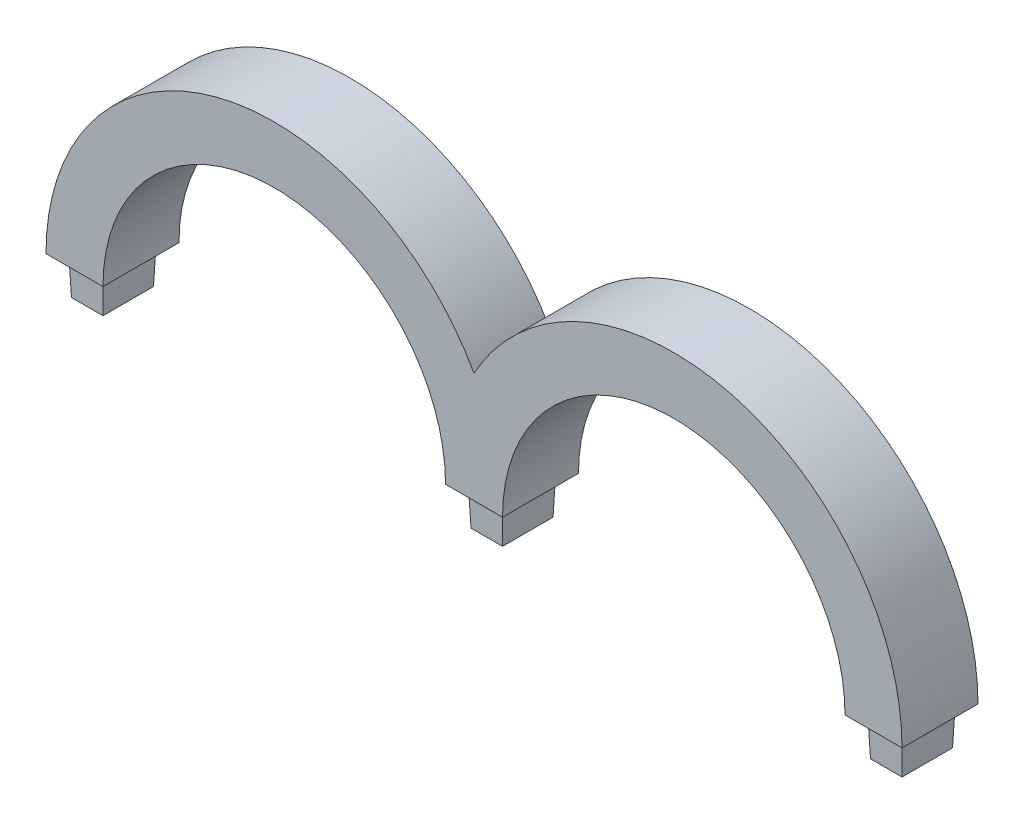
SolidWorks part; units mm, degrees
ref_plane "Front Plane" through (0, 0, 0) normal (0, 0, 1) x (1, 0, 0)
ref_plane "Top Plane" through (0, 0, 0) normal (0, 1, 0) x (1, 0, 0)
ref_plane "Right Plane" through (0, 0, 0) normal (1, 0, 0) x (0, 0, -1)
sketch "Sketch2" plane through (0, 0, 0) normal (0, 0, 1) x (1, 0, 0)
  line L0 (45.085, 0) -> (60.085, 0)
  line L1 (-45.085, 0) -> (150.255, 0) construction
  line L2 (52.585, 29.0693) -> (52.585, 29.0693)
  line L3 (-60.085, 0) -> (-45.085, 0)
  line L4 (150.255, 0) -> (165.255, 0)
  arc A0 (45.085, 0) -> (-45.085, 0) centre (0, 0) ccw
  arc A1 (150.255, 0) -> (60.085, 0) centre (105.17, 0) ccw
  arc A2 (165.255, 0) -> (52.585, 29.0693) centre (105.17, 0) ccw
  arc A3 (52.585, 29.0693) -> (-60.085, 0) centre (0, 0) ccw
  dimension "D1" = 90.17
  dimension "D2" = 15
  dimension "D3" = 15
extrude "Boss-Extrude1" add sketch "Sketch2" along normal blind 20
sketch "Sketch3" plane through (0, 0, 0) normal (0, -1, 0) x (1, 0, 0)
  line L52 (-57.085, 3) -> (-48.085, 3)
  line L53 (-57.085, 17) -> (-57.085, 3)
  line L54 (-48.085, 17) -> (-57.085, 17)
  line L55 (-48.085, 3) -> (-48.085, 17)
  line L56 (-57.085, 3) -> (-48.085, 3)
  line L57 (-57.085, 17) -> (-57.085, 3)
  line L58 (-48.085, 17) -> (-57.085, 17)
  line L59 (-48.085, 3) -> (-48.085, 17)
  line L70 (48.085, 3) -> (57.085, 3)
  line L71 (48.085, 17) -> (48.085, 3)
  line L72 (57.085, 17) -> (48.085, 17)
  line L73 (57.085, 3) -> (57.085, 17)
  line L74 (48.085, 3) -> (57.085, 3)
  line L75 (48.085, 17) -> (48.085, 3)
  line L76 (57.085, 17) -> (48.085, 17)
  line L77 (57.085, 3) -> (57.085, 17)
  line L88 (153.255, 3) -> (162.255, 3)
  line L89 (153.255, 17) -> (153.255, 3)
  line L90 (162.255, 17) -> (153.255, 17)
  line L91 (162.255, 3) -> (162.255, 17)
  line L92 (153.255, 3) -> (162.255, 3)
  line L93 (153.255, 17) -> (153.255, 3)
  line L94 (162.255, 17) -> (153.255, 17)
  line L95 (162.255, 3) -> (162.255, 17)
  dimension "D2" = 3
  dimension "D3" = 3
  dimension "D4" = 3
extrude "Boss-Extrude2" add sketch "Sketch3" along normal blind 10 draft 2
